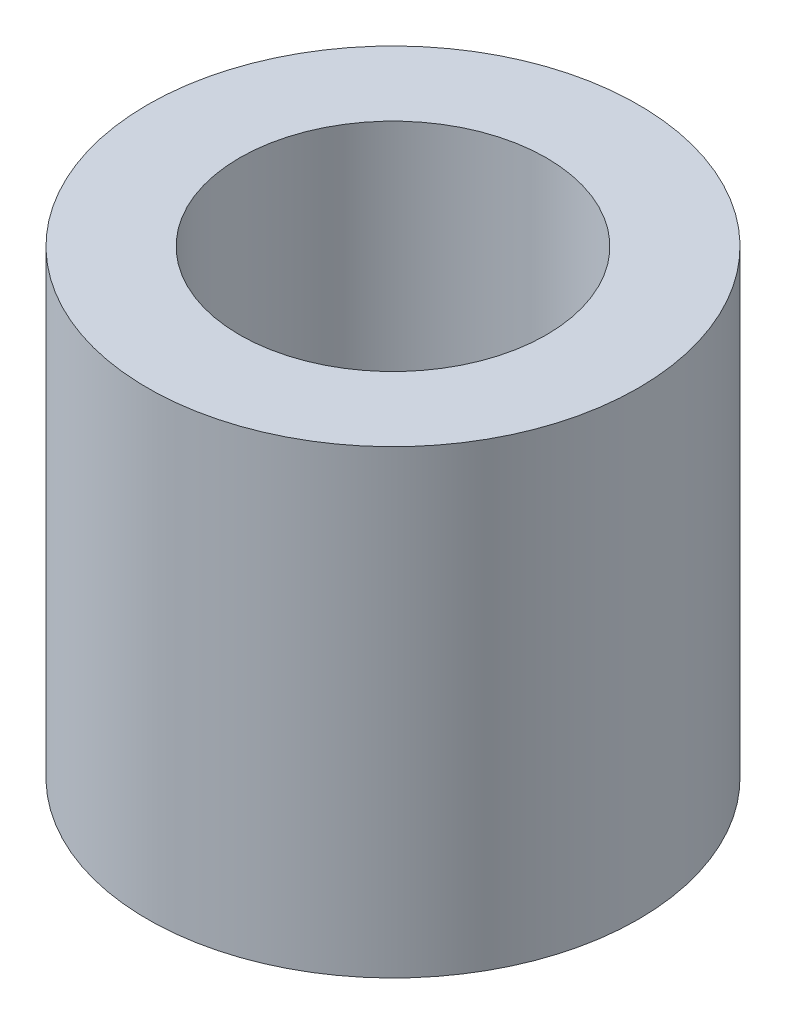
SolidWorks part; units mm, degrees
ref_plane "Спереди" through (0, 0, 0) normal (0, 0, 1) x (1, 0, 0)
ref_plane "Сверху" through (0, 0, 0) normal (0, 1, 0) x (1, 0, 0)
ref_plane "Справа" through (0, 0, 0) normal (1, 0, 0) x (0, 0, -1)
sketch "Эскиз1" plane through (0, 0, 0) normal (0, 1, 0) x (1, 0, 0)
  circle A0 centre (0, 0) radius 5
extrude "Вытянуть-Тонкостенный1" add sketch "Эскиз1" along normal blind 15 thin
